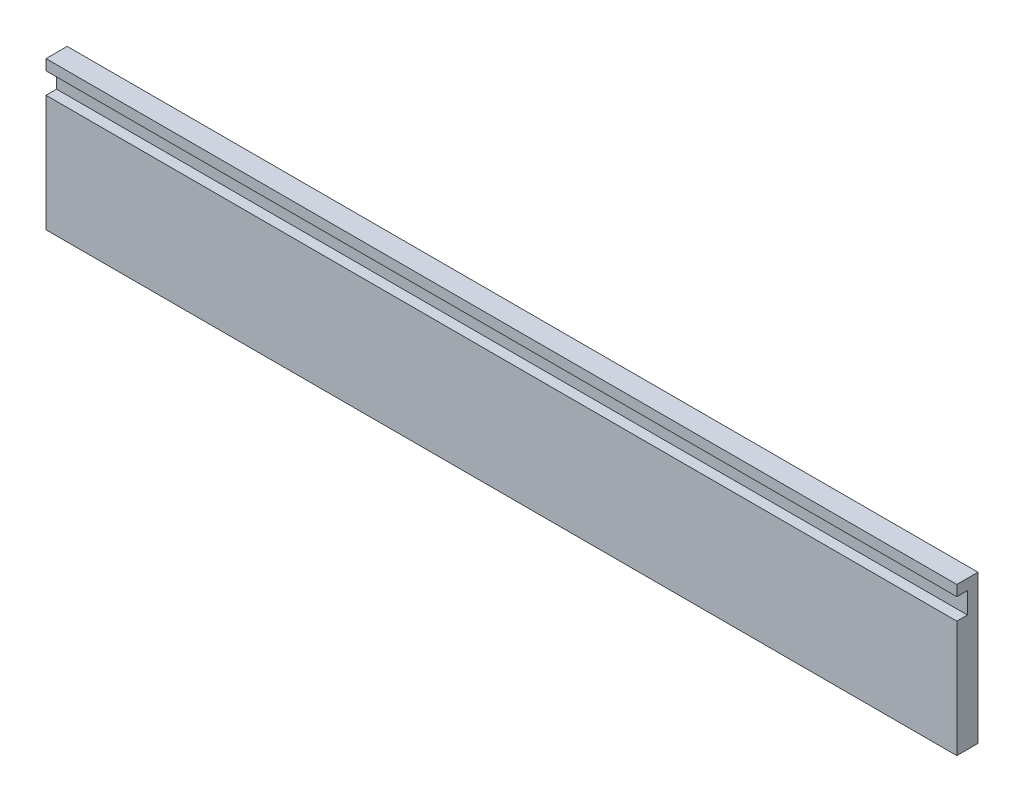
SolidWorks part; units mm, degrees
material "Cedar"
ref_plane "Front Plane" through (0, 0, 0) normal (0, 0, 1) x (1, 0, 0)
ref_plane "Top Plane" through (0, 0, 0) normal (0, 1, 0) x (1, 0, 0)
ref_plane "Right Plane" through (0, 0, 0) normal (1, 0, 0) x (0, 0, -1)
sketch "Sketch2" plane through (0, 0, 0) normal (0, 0, 1) x (1, 0, 0)
  line L1 (-214.4376, 94.2879) -> (331.6624, 94.2879)
  line L2 (-214.4376, 94.2879) -> (-214.4376, 5.3879)
  line L3 (-214.4376, 5.3879) -> (331.6624, 5.3879)
  line L4 (331.6624, 94.2879) -> (331.6624, 5.3879)
  dimension "D1" = 88.9
  dimension "D2" = 546.1
extrude "Boss-Extrude1" add sketch "Sketch2" along normal blind 12.7
sketch "Sketch3" plane through (0, 0, 12.7) normal (0, 0, 1) x (1, 0, 0)
  line L0 (-214.4376, 94.2879) -> (-214.4376, 5.3879) construction
  line L1 (-214.4376, 87.9379) -> (331.6624, 87.9379)
  line L2 (-214.4376, 87.9379) -> (-214.4376, 75.2379)
  line L3 (-214.4376, 75.2379) -> (331.6624, 75.2379)
  line L4 (331.6624, 87.9379) -> (331.6624, 75.2379)
  line L5 (331.6624, 5.3879) -> (331.6624, 94.2879) construction
  line L6 (331.6624, 94.2879) -> (-214.4376, 94.2879) construction
  dimension "D1" = 12.7
  dimension "D2" = 6.35
extrude "Cut-Extrude1" cut sketch "Sketch3" against normal blind 6.35
